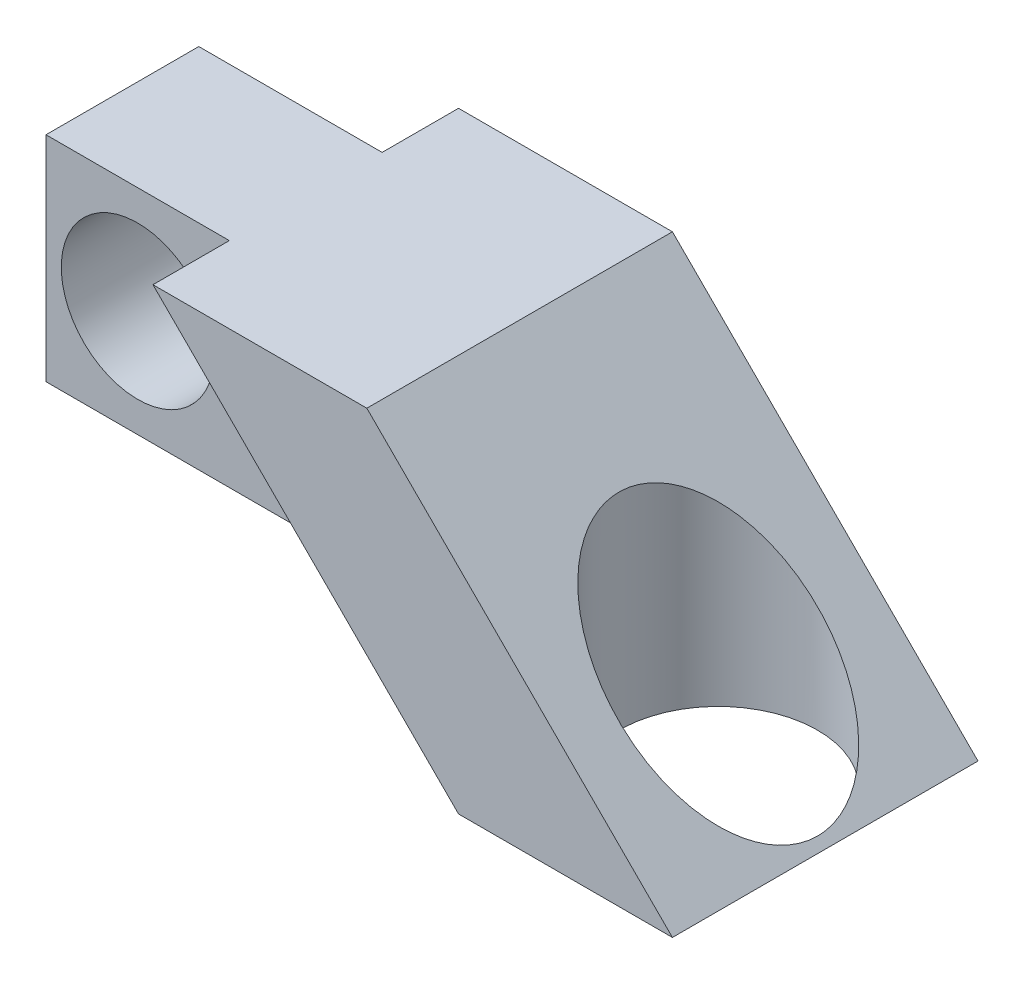
SolidWorks part; units mm, degrees
ref_plane "Front Plane" through (0, 0, 0) normal (0, 0, 1) x (1, 0, 0)
ref_plane "Top Plane" through (0, 0, 0) normal (0, 1, 0) x (1, 0, 0)
ref_plane "Right Plane" through (0, 0, 0) normal (1, 0, 0) x (0, 0, -1)
sketch "Sketch2" plane through (0, 0, 0) normal (0, 0, 1) x (1, 0, 0)
  line L0 (0, 0) -> (-7, 0)
  line L1 (0, 0) -> (-10, 10)
  line L2 (-7, 0) -> (-17, 10)
  line L3 (-10, 10) -> (-17, 10)
  dimension "D1" = 7
  dimension "D2" = 10
  dimension "D3" = 10
extrude "Boss-Extrude2" add sketch "Sketch2" along normal mid plane 10
sketch "Sketch3" plane through (0, 0, 0) normal (0, -1, 0) x (1, 0, 0)
  line L0 (-7, 0) -> (0, 0) construction
  line L1 (-7, 5) -> (-7, -5) construction
  circle A0 centre (-3.5, 0) radius 3.25
  point P7 (0, 0)
  point P8 (-3.5, 0)
  dimension "D1" = 6.5
extrude "Cut-Extrude1" cut sketch "Sketch3" against normal through all
sketch "Sketch4" plane through (0, 0, 0) normal (0, 0, 1) x (1, 0, 0)
  line L0 (-17, 10) -> (-7, 0) construction
  line L1 (-10, 3) -> (-23, 3)
  line L2 (-10, 3) -> (-10, 10)
  line L3 (-10, 10) -> (-23, 10)
  line L4 (-23, 3) -> (-23, 10)
  line L5 (-16.5, 10) -> (-16.5, 3) construction
  line L6 (-10, 6.5) -> (-23, 6.5) construction
  line L7 (-10, 10) -> (-17, 10) construction
  point P328 (-16.5, 6.5)
  dimension "D1" = 7
  dimension "D2" = 6
extrude "Boss-Extrude3" add sketch "Sketch4" along normal mid plane 5
sketch "Sketch5" plane through (0, 0, 2.5) normal (0, 0, 1) x (1, 0, 0)
  line L0 (-23, 10) -> (-23, 3) construction
  line L1 (-23, 6.5) -> (-13.5, 6.5) construction
  line L2 (-17, 10) -> (-10, 3) construction
  circle A0 centre (-20, 6.5) radius 2.5
  point P4 (0, 0)
  point P9 (-31.2516, 8.5127)
  dimension "D1" = 5
  dimension "D2" = 3
extrude "Cut-Extrude2" cut sketch "Sketch5" against normal through all
